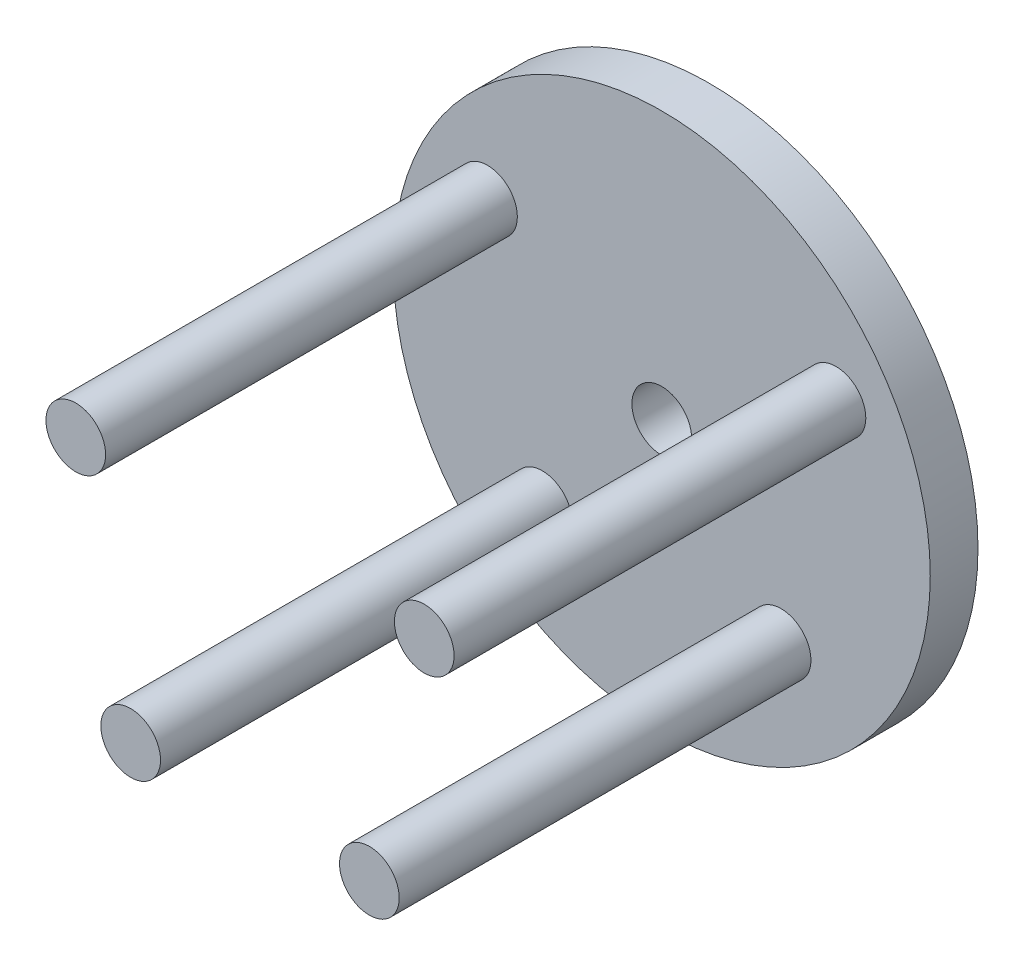
SolidWorks part; units mm, degrees
ref_plane "Front Plane" through (0, 0, 0) normal (0, 0, 1) x (1, 0, 0)
ref_plane "Top Plane" through (0, 0, 0) normal (0, 1, 0) x (1, 0, 0)
ref_plane "Right Plane" through (0, 0, 0) normal (1, 0, 0) x (0, 0, -1)
sketch "Sketch1" plane through (0, 0, 0) normal (0, 0, 1) x (1, 0, 0)
  circle A0 centre (0, 0) radius 28.575
  dimension "D1" = 57.15
extrude "Boss-Extrude1" add sketch "Sketch1" along normal blind 5.08
sketch "Sketch2" plane through (0, 0, 5.08) normal (0, 0, 1) x (1, 0, 0)
  line L0 (-18.542, 11.1125) -> (18.542, 11.1125) construction
  line L1 (0, 11.1125) -> (0, 0) construction
  line L2 (-28.1753, 4.7625) -> (28.1753, 4.7625) construction
  line L4 (19.05, -20.4756) -> (-19.05, -20.4756) construction
  line L5 (19.05, -20.4756) -> (19.05, -7.7756) construction
  line L6 (19.05, -7.7756) -> (-19.05, -7.7756) construction
  line L7 (-19.05, -20.4756) -> (-19.05, -7.7756) construction
  line L8 (19.05, -20.4756) -> (-19.05, -7.7756) construction
  line L9 (19.05, -7.7756) -> (-19.05, -20.4756) construction
  circle A0 centre (-18.542, 11.1125) radius 6.35 construction
  circle A1 centre (-18.542, 11.1125) radius 3.175
  circle A2 centre (18.542, 11.1125) radius 3.175
  circle A3 centre (-12.7, -14.1256) radius 3.175
  circle A4 centre (12.7, -14.1256) radius 3.175
  circle A5 centre (0, 0) radius 28.575 construction
  circle A6 centre (0, 0) radius 3.175 construction
  circle A7 centre (0, 0) radius 27.967 construction
  point P17 (0, -14.1256)
  dimension "D1" = 6.35
  dimension "D3" = 12.7
  dimension "D6" = 6.35
  dimension "D10" = 6.35
  dimension "D2" = 37.084
  dimension "D4" = 4.7625
  dimension "D5" = 6.35
  dimension "D9" = 25.4
  dimension "D11" = 6.35
  dimension "D12" = 12.7
  dimension "D13" = 6.35
extrude "Boss-Extrude2" add sketch "Sketch2" along normal blind 43.815
sketch "Sketch6" plane through (0, 0, 0) normal (0, 0, -1) x (-1, 0, 0)
  circle A0 centre (0, 0) radius 3.175
  dimension "D1" = 6.35
extrude "Cut-Extrude2" cut sketch "Sketch6" against normal through all
